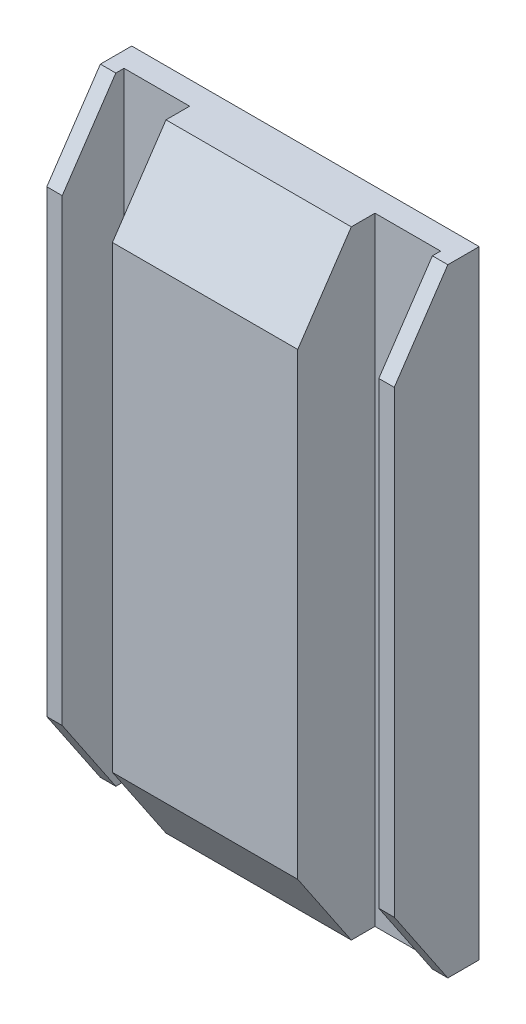
SolidWorks part; units mm, degrees
ref_plane "Front Plane" through (0, 0, 0) normal (0, 0, 1) x (1, 0, 0)
ref_plane "Top Plane" through (0, 0, 0) normal (0, 1, 0) x (1, 0, 0)
ref_plane "Right Plane" through (0, 0, 0) normal (1, 0, 0) x (0, 0, -1)
sketch "Sketch1" plane through (0, 0, 0) normal (0, 0, 1) x (1, 0, 0)
  line L1 (40.0897, 88.3073) -> (154.3897, 88.3073)
  line L2 (40.0897, 88.3073) -> (40.0897, -114.8927)
  line L3 (40.0897, -114.8927) -> (154.3897, -114.8927)
  line L4 (154.3897, 88.3073) -> (154.3897, -114.8927)
  dimension "D1" = 203.2
  dimension "D2" = 114.3
extrude "Boss-Extrude1" add sketch "Sketch1" along normal blind 33.02
sketch "Sketch2" plane through (0, 88.3073, 0) normal (0, 1, 0) x (1, 0, 0)
  line L0 (40.0897, -33.02) -> (40.0897, 0) construction
  line L1 (40.0897, -7.62) -> (66.7597, -7.62)
  line L2 (40.0897, -7.62) -> (40.0897, -33.02)
  line L3 (40.0897, -33.02) -> (66.7597, -33.02)
  line L4 (66.7597, -7.62) -> (66.7597, -33.02)
  line L5 (154.3897, -33.02) -> (40.0897, -33.02) construction
  line L6 (154.3897, -33.02) -> (154.3897, 0) construction
  line L7 (154.3897, -7.62) -> (127.7197, -7.62)
  line L8 (154.3897, -7.62) -> (154.3897, -33.02)
  line L9 (154.3897, -33.02) -> (127.7197, -33.02)
  line L10 (127.7197, -7.62) -> (127.7197, -33.02)
  dimension "D1" = 25.4
  dimension "D2" = 26.67
extrude "Cut-Extrude1" cut sketch "Sketch2" against normal through all
chamfer "Chamfer1" distance 17.62 angle 56 2 edges at (97.2397, 88.3073, 33.02) (97.2397, -114.8927, 33.02)
sketch "Sketch3" plane through (0, 0, 7.62) normal (0, 0, 1) x (1, 0, 0)
  line L0 (66.7597, -114.8927) -> (40.0897, -114.8927) construction
  line L1 (40.0897, 88.3073) -> (45.1697, 88.3073)
  line L2 (40.0897, 88.3073) -> (40.0897, -114.8927)
  line L3 (40.0897, -114.8927) -> (45.1697, -114.8927)
  line L4 (45.1697, 88.3073) -> (45.1697, -114.8927)
  line L5 (154.3897, 88.3073) -> (127.7197, 88.3073) construction
  line L6 (154.3897, -114.8927) -> (149.3097, -114.8927)
  line L7 (154.3897, -114.8927) -> (154.3897, 88.3073)
  line L8 (154.3897, 88.3073) -> (149.3097, 88.3073)
  line L9 (149.3097, -114.8927) -> (149.3097, 88.3073)
  dimension "D1" = 5.08
extrude "Boss-Extrude2" add sketch "Sketch3" along normal blind 20.32
chamfer "Chamfer2" distance 17.62 angle 56 4 edges at (42.6297, -114.8927, 27.94) (151.8497, -114.8927, 27.94) (42.6297, 88.3073, 27.94) (151.8497, 88.3073, 27.94)
sketch "Sketch5" plane through (0, 0, 0) normal (0, 0, -1) x (-1, 0, 0)
  line L0 (-154.3897, 88.3073) -> (-40.0897, 88.3073) construction
  line L1 (-135.3397, 62.9073) -> (-59.1397, 62.9073)
  line L2 (-135.3397, 62.9073) -> (-135.3397, -13.2927)
  line L3 (-135.3397, -13.2927) -> (-59.1397, -13.2927)
  line L4 (-59.1397, 62.9073) -> (-59.1397, -13.2927)
  point P4 (-97.2397, 62.9073)
  point P7 (-97.2397, 88.3073)
  dimension "D1" = 76.2
  dimension "D2" = 76.2
  dimension "D3" = 25.4
extrude "Cut-Extrude2" cut sketch "Sketch5" against normal blind 2.54
